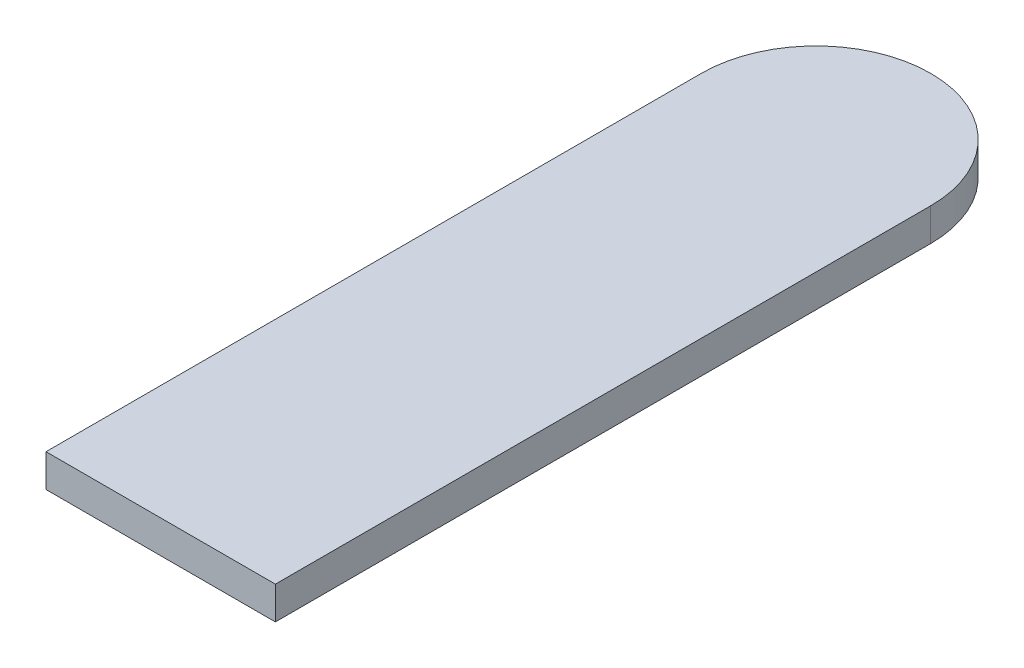
SolidWorks part; units mm, degrees
ref_plane "Front Plane" through (0, 0, 0) normal (0, 0, 1) x (1, 0, 0)
ref_plane "Top Plane" through (0, 0, 0) normal (0, 1, 0) x (1, 0, 0)
ref_plane "Right Plane" through (0, 0, 0) normal (1, 0, 0) x (0, 0, -1)
sketch "Sketch1" plane through (0, 0, 0) normal (0, 1, 0) x (1, 0, 0)
  line L0 (0, 0) -> (-7, 0)
  line L1 (-7, 0) -> (-7, 20)
  line L2 (0, 0) -> (0, 20)
  arc A0 (-7, 20) -> (0, 20) centre (-3.5, 20) cw
extrude "Boss-Extrude1" add sketch "Sketch1" along normal blind 1
